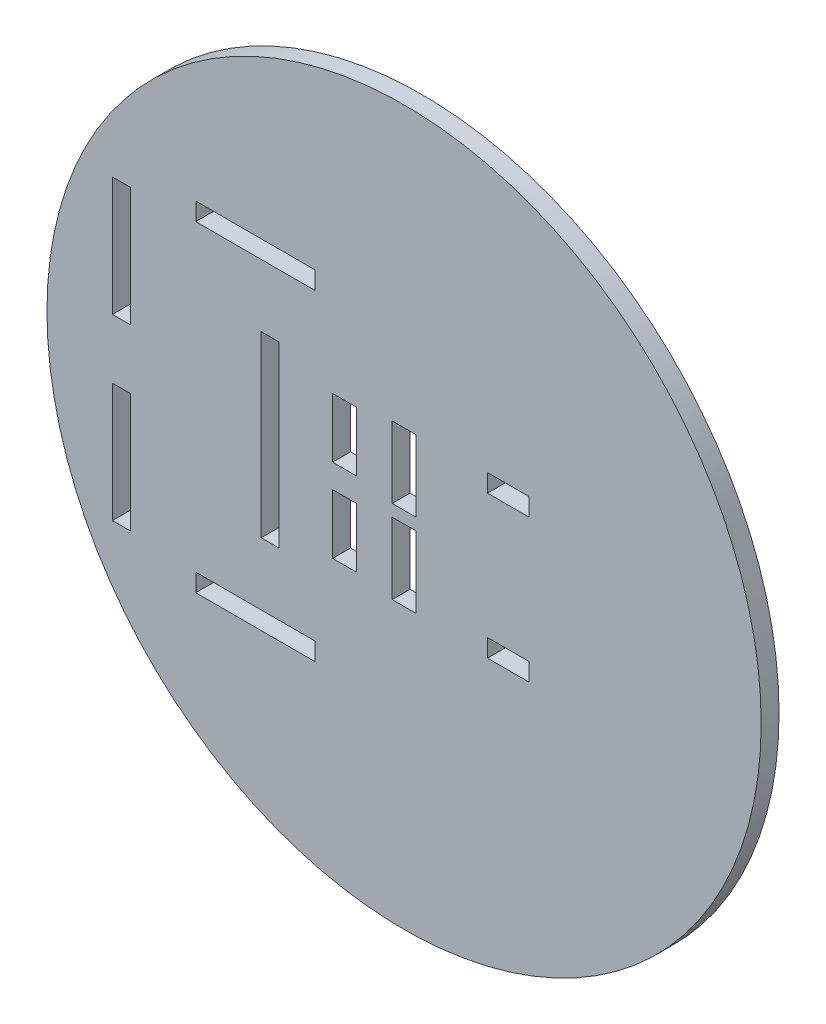
SolidWorks part; units mm, degrees
ref_plane "Front Plane" through (0, 0, 0) normal (0, 0, 1) x (1, 0, 0)
ref_plane "Top Plane" through (0, 0, 0) normal (0, 1, 0) x (1, 0, 0)
ref_plane "Right Plane" through (0, 0, 0) normal (1, 0, 0) x (0, 0, -1)
sketch "Sketch1" plane through (0, 0, 0) normal (0, 0, 1) x (1, 0, 0)
  line L0 (0, 0) -> (0, 79.8631) construction
  line L1 (0, 0) -> (124.6897, 0) construction
  line L2 (-20, 30) -> (-50, 30)
  line L3 (-20, 30) -> (-20, -30)
  line L4 (-20, -30) -> (-50, -30)
  line L5 (-50, 30) -> (-50, -30)
  line L6 (10, 15) -> (25.0129, 15)
  line L7 (10, 15) -> (10, -15)
  line L8 (10, -15) -> (25.0129, -15)
  line L9 (25.0129, 15) -> (25.0129, -15)
  line L11 (-35, -25.5) -> (-15, -25.5)
  line L12 (-35, -25.5) -> (-35, -28.5)
  line L13 (-35, -28.5) -> (-15, -28.5)
  line L14 (-15, -25.5) -> (-15, -28.5)
  line L15 (-49, 25) -> (-46, 25)
  line L16 (-49, 25) -> (-49, 5)
  line L17 (-49, 5) -> (-46, 5)
  line L18 (-46, 25) -> (-46, 5)
  line L19 (-49, -5) -> (-46, -5)
  line L20 (-49, -5) -> (-49, -25)
  line L21 (-49, -25) -> (-46, -25)
  line L22 (-46, -5) -> (-46, -25)
  line L23 (-24, 15) -> (-21, 15)
  line L24 (-24, 15) -> (-24, -15)
  line L25 (-24, -15) -> (-21, -15)
  line L26 (-21, 15) -> (-21, -15)
  line L27 (-35, 28.5) -> (-15, 28.5)
  line L28 (-35, 28.5) -> (-35, 25.5)
  line L29 (-35, 25.5) -> (-15, 25.5)
  line L30 (-15, 28.5) -> (-15, 25.5)
  line L31 (14.0194, -10.5) -> (21.0129, -10.5)
  line L32 (14.0194, -10.5) -> (14.0194, -13.5)
  line L33 (14.0194, -13.5) -> (21.0129, -13.5)
  line L34 (21.0129, -10.5) -> (21.0129, -13.5)
  line L35 (14.0194, 10.5) -> (21.0129, 10.5)
  line L36 (14.0194, 10.5) -> (14.0194, 13.5)
  line L37 (14.0194, 13.5) -> (21.0129, 13.5)
  line L38 (21.0129, 10.5) -> (21.0129, 13.5)
  line L39 (-2, 13) -> (2, 13)
  line L40 (-2, 13) -> (-2, 1)
  line L41 (-2, 1) -> (2, 1)
  line L42 (2, 13) -> (2, 1)
  line L43 (-2, 13) -> (2, 1) construction
  line L44 (-2, 1) -> (2, 13) construction
  line L45 (-2, -1) -> (2, -1)
  line L46 (-2, -1) -> (-2, -13)
  line L47 (-2, -13) -> (2, -13)
  line L48 (2, -1) -> (2, -13)
  line L49 (-2, -1) -> (2, -13) construction
  line L50 (-2, -13) -> (2, -1) construction
  line L51 (-12, 12) -> (-8, 12)
  line L52 (-12, 12) -> (-12, 2)
  line L53 (-12, 2) -> (-8, 2)
  line L54 (-8, 12) -> (-8, 2)
  line L55 (-12, 12) -> (-8, 2) construction
  line L56 (-12, 2) -> (-8, 12) construction
  line L57 (-12, -2) -> (-8, -2)
  line L58 (-12, -2) -> (-12, -12)
  line L59 (-12, -12) -> (-8, -12)
  line L60 (-8, -2) -> (-8, -12)
  line L61 (-12, -2) -> (-8, -12) construction
  line L62 (-12, -12) -> (-8, -2) construction
  circle A0 centre (0, 0) radius 60
  point P3 (0, 7)
  point P48 (0, -7)
  point P53 (-10, 7)
  point P58 (-10, -7)
  dimension "D1" = 120
  dimension "D3" = 30
  dimension "D4" = 30
  dimension "D5" = 20
  dimension "D6" = 30
  dimension "D7" = 10
  dimension "D8" = 15.0129
  dimension "D9" = 15
  dimension "D10" = 15
  dimension "D11" = 1
  dimension "D12" = 3
  dimension "D13" = 20
  dimension "D14" = 5
  dimension "D15" = 1
  dimension "D16" = 20
  dimension "D17" = 5
  dimension "D18" = 3
  dimension "D19" = 1
  dimension "D20" = 3
  dimension "D21" = 15
  dimension "D22" = 30
  dimension "D23" = 1.5
  dimension "D24" = 15
  dimension "D25" = 3
  dimension "D26" = 15
  dimension "D27" = 15
  dimension "D28" = 1.5
  dimension "D29" = 3
  dimension "D30" = 15
  dimension "D31" = 4.0194
  dimension "D32" = 1.5
  dimension "D33" = 3
  dimension "D34" = 4
  dimension "D35" = 4.0194
  dimension "D36" = 4
  dimension "D37" = 1.5
  dimension "D38" = 3
  dimension "D39" = 12
  dimension "D40" = 12
  dimension "D41" = 4
  dimension "D42" = 4
  dimension "D43" = 1
  dimension "D44" = 1
  dimension "D45" = 10
  dimension "D46" = 4
  dimension "D47" = 4
  dimension "D48" = 10
  dimension "D49" = 10
  dimension "D50" = 10
extrude "Boss-Extrude1" add sketch "Sketch1" along normal mid plane 3 contours A0 L27 L30 L29 L3 L11 L14 L13 L4 L5 L2 L6 L9 L8 L7 | L29 L28 L27 L3 L2 L5 L4 L13 L12 L11 L15 L18 L17 L16 L19 L22 L21 L20 L23 L26 L25 L24 | L9 L6 L7 L8 L38 L35 L36 L37 L31 L34 L33 L32
ref_plane "Plane1" through (0, 0, 1.5) normal (0, 0, 1) x (1, 0, 0)
sketch "Sketch3" plane through (0, 0, 1.5) normal (0, 0, 1) x (1, 0, 0)
  point P0 (0, 0)
